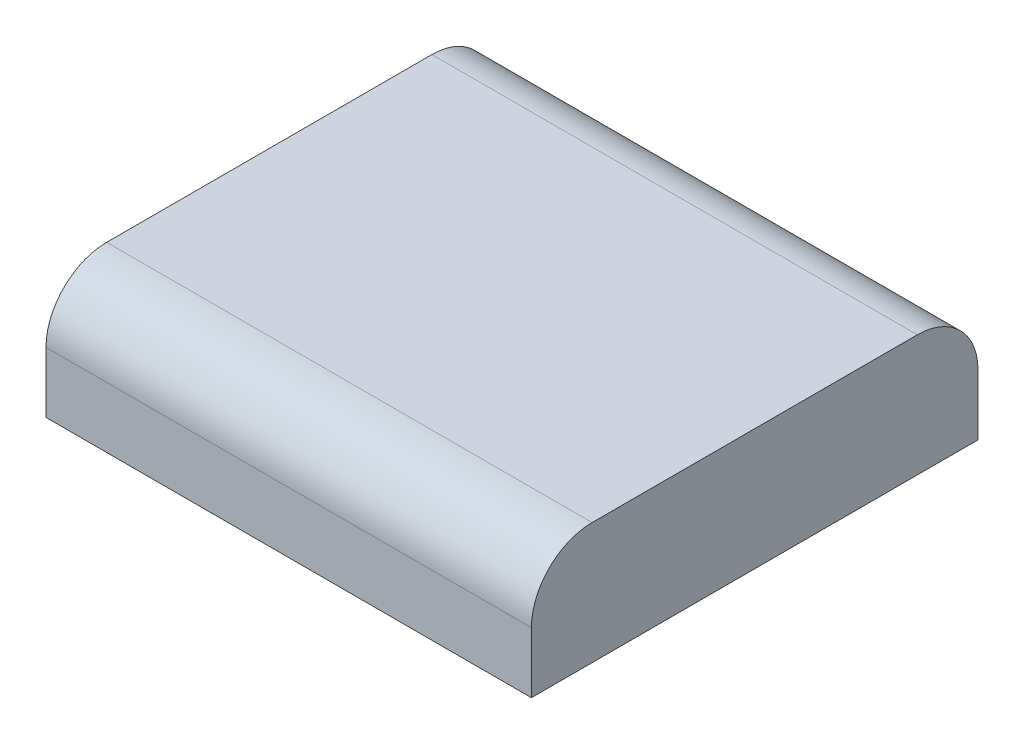
SolidWorks part; units mm, degrees
ref_plane "Front Plane" through (0, 0, 0) normal (0, 0, 1) x (1, 0, 0)
ref_plane "Top Plane" through (0, 0, 0) normal (0, 1, 0) x (1, 0, 0)
ref_plane "Right Plane" through (0, 0, 0) normal (1, 0, 0) x (0, 0, -1)
sketch "Sketch1" plane through (0, 0, 0) normal (0, 1, 0) x (1, 0, 0)
  line L1 (-31.75, -29.21) -> (31.75, -29.21)
  line L2 (-31.75, -29.21) -> (-31.75, 29.21)
  line L3 (-31.75, 29.21) -> (31.75, 29.21)
  line L4 (31.75, -29.21) -> (31.75, 29.21)
  line L5 (-31.75, -29.21) -> (31.75, 29.21) construction
  line L6 (-31.75, 29.21) -> (31.75, -29.21) construction
  point P0 (0, 0)
  dimension "D1" = 63.5
  dimension "D2" = 58.42
extrude "Boss-Extrude1" add sketch "Sketch1" along normal blind 15.875
fillet "Fillet1" radius 7.9375 2 edges at (0, 15.875, -29.21) (0, 15.875, 29.21)
